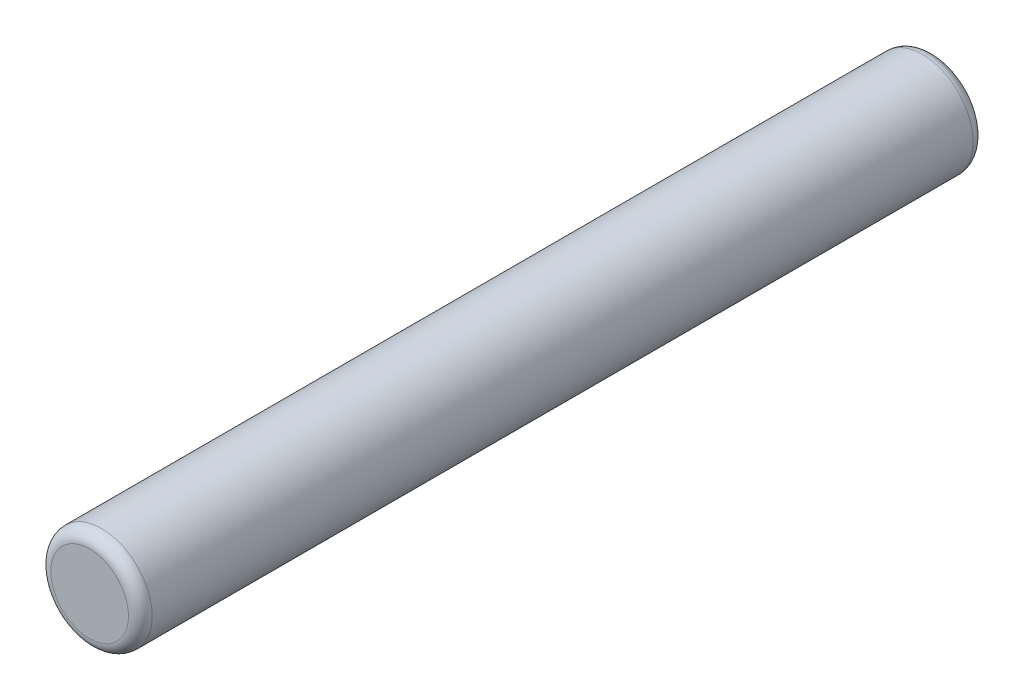
SolidWorks part; units mm, degrees
ref_plane "Front" through (0, 0, 0) normal (0, 0, 1) x (1, 0, 0)
ref_plane "Top" through (0, 0, 0) normal (0, 1, 0) x (1, 0, 0)
ref_plane "Right" through (0, 0, 0) normal (1, 0, 0) x (0, 0, -1)
sketch "Sketch1" plane through (0, 0, 0) normal (0, 0, 1) x (1, 0, 0)
  circle A0 centre (0, 0) radius 1.5
  dimension "D1" = 3
extrude "Boss-Extrude1" add sketch "Sketch1" along normal mid plane 25
fillet "Fillet1" radius 0.35 2 edges at (1.5, 0, -12.5) (1.5, 0, 12.5)
